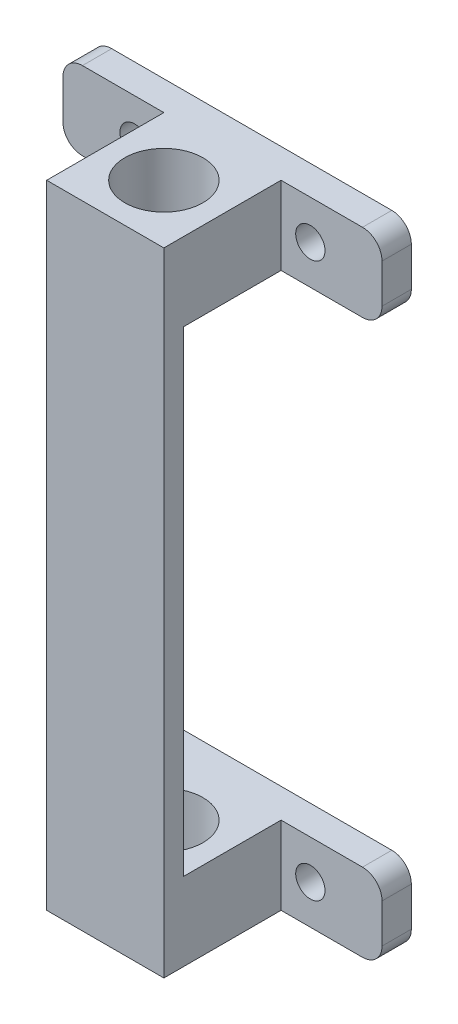
SolidWorks part; units mm, degrees
ref_plane "前视基准面" through (0, 0, 0) normal (0, 0, 1) x (1, 0, 0)
ref_plane "上视基准面" through (0, 0, 0) normal (0, 1, 0) x (1, 0, 0)
ref_plane "右视基准面" through (0, 0, 0) normal (1, 0, 0) x (0, 0, -1)
sketch "草图1" plane through (0, 0, 0) normal (0, 0, 1) x (1, 0, 0)
  line L0 (12.612, 26.3586) -> (-20.0654, 26.3586) construction
  line L2 (-20.0654, 30.3586) -> (12.612, 30.3586)
  line L3 (-20.0654, 30.3586) -> (-20.0654, 22.3586)
  line L4 (-20.0654, 22.3586) -> (12.612, 22.3586)
  line L5 (12.612, 30.3586) -> (12.612, 22.3586)
  line L6 (-20.0654, 30.3586) -> (12.612, 22.3586) construction
  line L7 (-20.0654, 22.3586) -> (12.612, 30.3586) construction
  point P4 (-3.7267, 26.3586)
extrude "凸台-拉伸1" add sketch "草图1" against normal blind 3
sketch "草图2" plane through (0, 0, 0) normal (0, 0, 1) x (1, 0, 0)
  line L0 (-3.7267, 30.3586) -> (-3.7267, 22.3586) construction
  line L3 (12.612, 30.3586) -> (-20.0654, 30.3586) construction
  line L4 (-20.0654, 22.3586) -> (12.612, 22.3586) construction
  line L5 (-3.7267, 26.3586) -> (5.2733, 26.3586) construction
  line L6 (-3.7267, 26.3586) -> (-12.7267, 26.3586) construction
  circle A2 centre (-12.7267, 26.3586) radius 1.5
  circle A3 centre (5.2733, 26.3586) radius 1.5
extrude "切除-拉伸1" cut sketch "草图2" against normal through all
sketch "草图3" plane through (0, 22.3586, 0) normal (0, -1, 0) x (1, 0, 0)
  line L0 (-20.0654, 0) -> (12.612, 0) construction
  line L1 (-3.7267, 0) -> (-3.7267, 6) construction
  circle A0 centre (-3.7267, 6) radius 6
  point P0 (-3.7267, 0)
extrude "凸台-拉伸2" add sketch "草图3" against normal up to surface (8 mm away) separate body up to face at (-3.7267, 30.3586, -1.5)
sketch "草图5" plane through (0, 22.3586, 0) normal (0, -1, 0) x (1, 0, 0)
  line L0 (-9.7267, 6) -> (-9.7267, 0)
  line L1 (-20.0654, 0) -> (12.612, 0) construction
  line L2 (-9.7267, 0) -> (-3.7267, 0)
  line L3 (-3.7267, 0) -> (-9.7267, 6)
  line L4 (-3.7267, 0) -> (2.2733, 6)
  line L5 (2.2733, 6) -> (2.2733, 0)
  line L6 (2.2733, 0) -> (-3.7267, 0)
  circle A0 centre (-3.7267, 6) radius 6 construction
extrude "凸台-拉伸3" add sketch "草图5" against normal up to surface (8 mm away) contours L3 L0 L2 | L4 L5 L6 up to face at (-9.7267, 30.3586, 6)
ref_plane "基准面1" through (0, 0, 6) normal (0, 0, -1) x (-1, 0, 0)
mirror "镜向1" about plane through (0, 0, 6) normal (0, 0, -1) of "凸台-拉伸3"
sketch "草图10" plane through (0, 0, 12) normal (0, 0, 1) x (1, 0, 0)
  line L1 (-9.7267, 22.3586) -> (2.2733, 22.3586)
  line L2 (-9.7267, 22.3586) -> (-9.7267, -2.0114)
  line L3 (-9.7267, -2.0114) -> (2.2733, -2.0114)
  line L4 (2.2733, 22.3586) -> (2.2733, -2.0114)
  line L5 (2.2733, 30.3586) -> (2.2733, 22.3586) construction
  line L6 (-9.7267, 22.3586) -> (2.2733, 22.3586) construction
  line L7 (-9.7267, 22.3586) -> (2.2733, 22.3586) construction
  point P8 (0, 0)
  point P9 (-9.7267, 22.6509)
extrude "凸台-拉伸5" add sketch "草图10" against normal blind 2
sketch "草图4" plane through (0, 22.3586, 0) normal (0, -1, 0) x (1, 0, 0)
  circle A0 centre (-3.7267, 6) radius 4
extrude "切除-拉伸2" cut sketch "草图4" against normal through all
fillet "圆角1" radius 2 4 edges at (12.612, 22.3586, -1.5) (12.612, 30.3586, -1.5) (-20.0654, 22.3586, -1.5) (-20.0654, 30.3586, -1.5)
mirror "镜向3" about plane through (-9.7267, -2.0114, 10) normal (0, -1, 0) of "圆角1", "凸台-拉伸1", "切除-拉伸1", "凸台-拉伸2", "切除-拉伸2", "凸台-拉伸3", "镜向1", "凸台-拉伸5"
